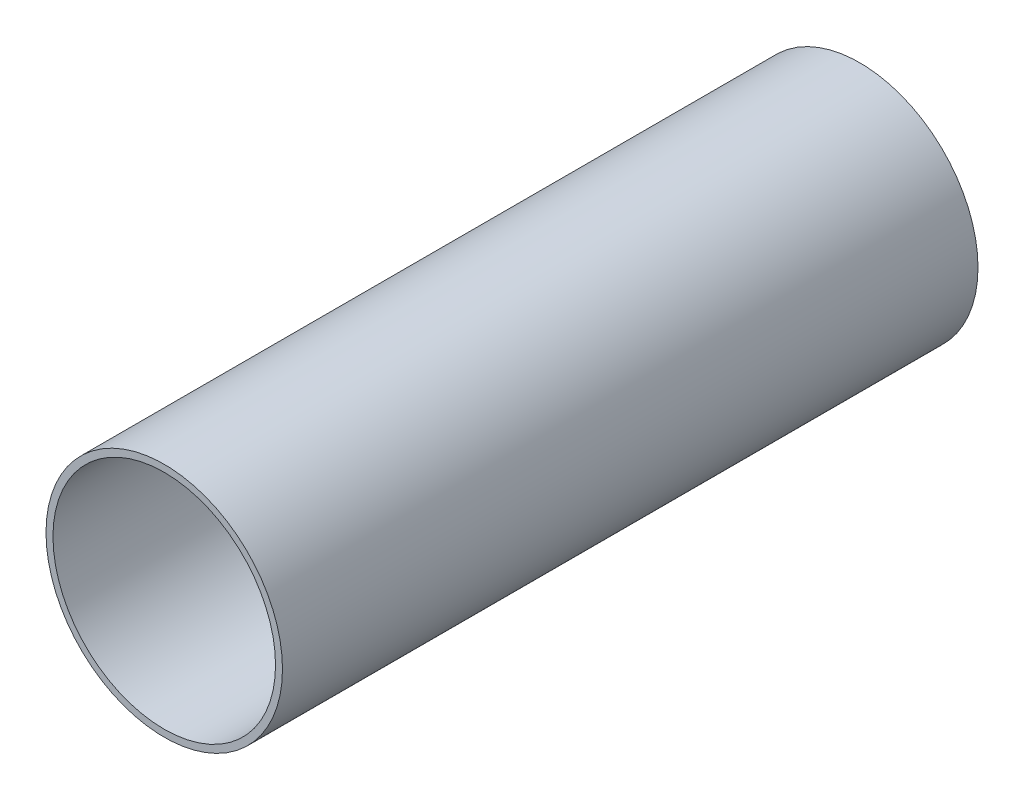
SolidWorks part; units mm, degrees
ref_plane "Front Plane" through (0, 0, 0) normal (0, 0, 1) x (1, 0, 0)
ref_plane "Top Plane" through (0, 0, 0) normal (0, 1, 0) x (1, 0, 0)
ref_plane "Right Plane" through (0, 0, 0) normal (1, 0, 0) x (0, 0, -1)
sketch "Sketch1" plane through (0, 0, 0) normal (0, 0, 1) x (1, 0, 0)
  circle A0 centre (0, 0) radius 4.25
  circle A1 centre (0, 0) radius 4
  dimension "D1" = 8
  dimension "D2" = 8.5
extrude "Boss-Extrude1" add sketch "Sketch1" along normal blind 25
